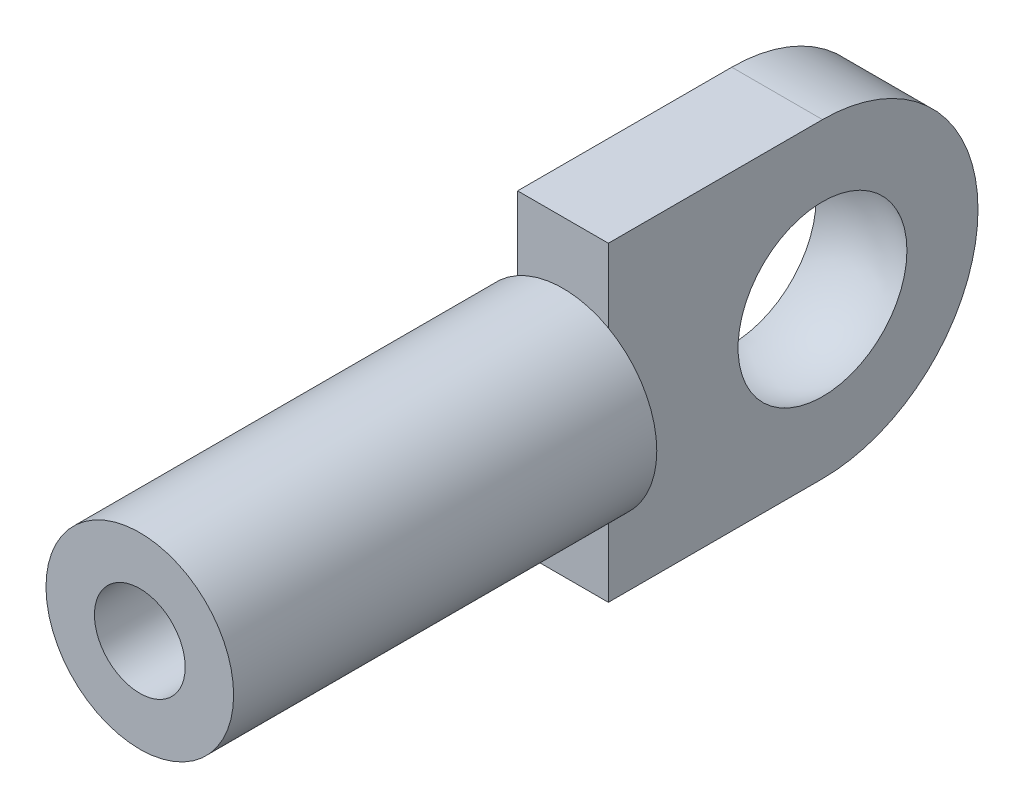
SolidWorks part; units mm, degrees
material "Nylon 6/10"
ref_plane "Front Plane" through (0, 0, 0) normal (0, 0, 1) x (1, 0, 0)
ref_plane "Top Plane" through (0, 0, 0) normal (0, 1, 0) x (1, 0, 0)
ref_plane "Right Plane" through (0, 0, 0) normal (1, 0, 0) x (0, 0, -1)
sketch "Sketch1" plane through (0, 0, 0) normal (0, 0, 1) x (1, 0, 0)
  circle A0 centre (0, 0) radius 2.3368
extrude "Extrude1" add sketch "Sketch1" along normal blind 10.541
sketch "Sketch2" plane through (0, 0, 0) normal (1, 0, 0) x (0, 0, -1)
  line L0 (0, 0) -> (0, 3.8735)
  line L1 (0, 0) -> (0, -3.8735)
  line L2 (5.334, 3.8735) -> (0, 3.8735)
  line L3 (5.334, -3.8735) -> (0, -3.8735)
  arc A0 (5.334, -3.8735) -> (5.334, 3.8735) centre (5.334, 0) ccw
extrude "Extrude2" add sketch "Sketch2" along normal blind 1.1303 and the other way blind 1.1303
sketch "Sketch3" plane through (0, 0, 0) normal (1, 0, 0) x (0, 0, -1)
  line L0 (5.334, 2.3876) -> (5.334, -2.3876)
  arc A0 (5.334, 2.3876) -> (5.334, -2.3876) centre (5.334, 0) ccw
revolve "Cut-Revolve1" cut sketch "Sketch3" angle 360 about L0
sketch "Sketch4" plane through (0, 0, 10.541) normal (0, 0, 1) x (1, 0, 0)
  circle A0 centre (0, 0) radius 1.1303
extrude "Extrude3" cut sketch "Sketch4" against normal blind 8.001
sketch "Sketch6" plane through (0, 0, 0) normal (1, 0, 0) x (0, 0, -1)
  line L0 (5.334, 0) -> (5.334, 2.569) construction
  line L1 (5.334, -1.4243) -> (5.334, 2.8486) construction
